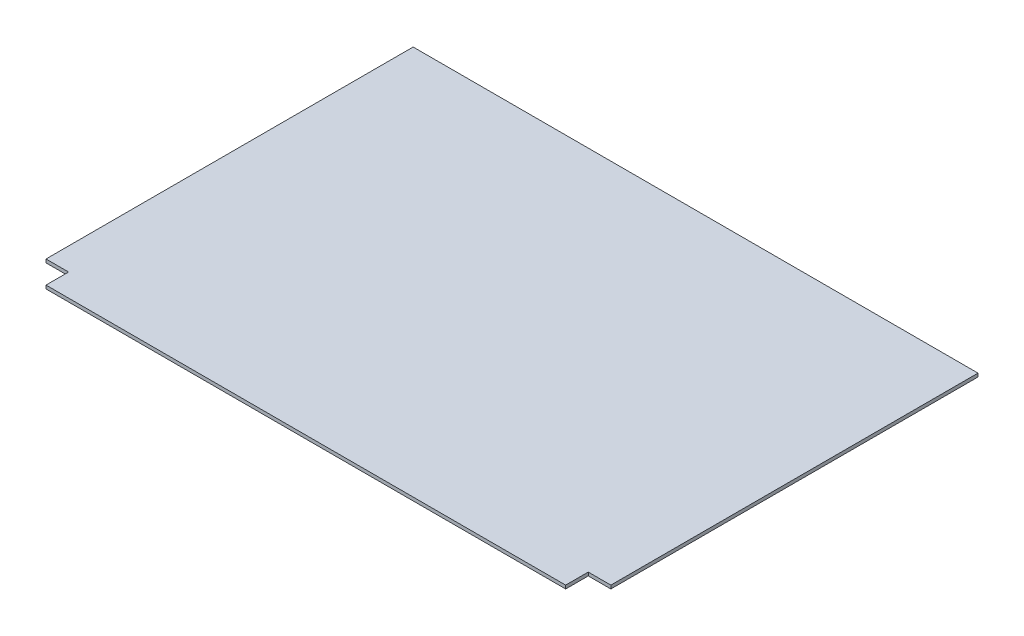
SolidWorks part; units mm, degrees
ref_plane "Front Plane" through (0, 0, 0) normal (0, 0, 1) x (1, 0, 0)
ref_plane "Top Plane" through (0, 0, 0) normal (0, 1, 0) x (1, 0, 0)
ref_plane "Right Plane" through (0, 0, 0) normal (1, 0, 0) x (0, 0, -1)
sketch "Sketch1" plane through (0, 0, 0) normal (0, 1, 0) x (1, 0, 0)
  line L3 (250, -155) -> (230, -155)
  line L4 (230, -155) -> (230, -175)
  line L5 (230, -175) -> (-230, -175)
  line L6 (-230, -175) -> (-230, -155)
  line L7 (-230, -155) -> (-250, -155)
  line L9 (250, 170) -> (-250, 170)
  line L10 (-250, 170) -> (-250, -155)
  line L11 (250, 170) -> (250, -155)
extrude "Boss-Extrude1" add sketch "Sketch1" along normal blind 3
